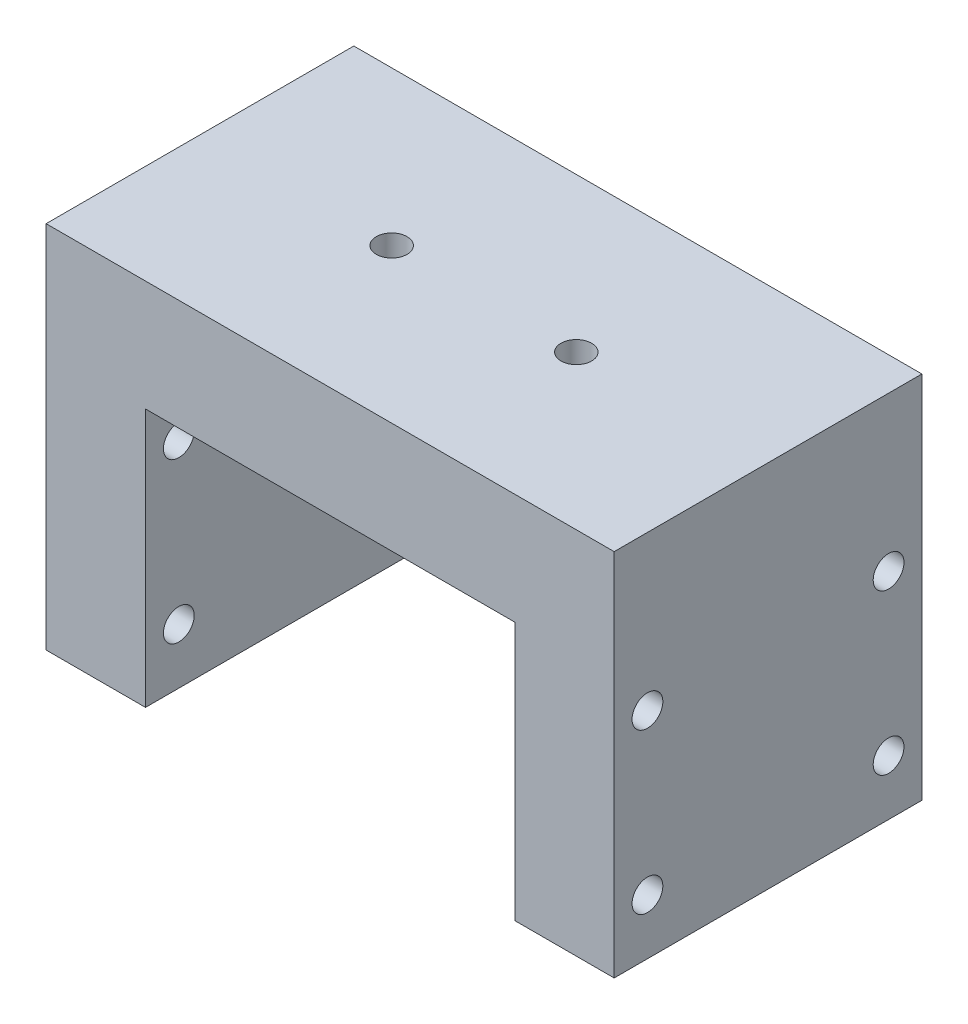
SolidWorks part; units mm, degrees
material "6061 Alloy"
ref_plane "Front Plane" through (0, 0, 0) normal (0, 0, 1) x (1, 0, 0)
ref_plane "Top Plane" through (0, 0, 0) normal (0, 1, 0) x (1, 0, 0)
ref_plane "Right Plane" through (0, 0, 0) normal (1, 0, 0) x (0, 0, -1)
sketch "Sketch2" plane through (0, 0, 0) normal (0, 0, 1) x (1, 0, 0)
  line L0 (-23.075, -21) -> (-23.075, 9)
  line L1 (-23.075, 9) -> (23.075, 9)
  line L2 (23.075, 9) -> (23.075, -21)
  line L3 (23.075, -21) -> (15, -21)
  line L4 (15, -21) -> (15, 0)
  line L5 (15, 0) -> (-15, 0)
  line L6 (-15, 0) -> (-15, -21)
  line L7 (-15, -21) -> (-23.075, -21)
  point P2 (0, 0)
  dimension "D1" = 30
  dimension "D2" = 21
  dimension "D3" = 46.15
  dimension "D4" = 30
extrude "Boss-Extrude1" add sketch "Sketch2" along normal mid plane 25
hole_wizard "M3x0.5 Tapped Hole1" positions "Sketch3" profile "Sketch4" tap size "M3x0.5" standard "ANSI Metric"
sketch "Sketch3" plane through (0, 9, 0) normal (0, 1, 0) x (1, 0, 0)
  line L0 (-7.5, 0) -> (7.5, 0) construction
  point P0 (-7.5, 0)
  point P2 (7.5, 0)
  point P9 (0, 0)
  dimension "D1" = 15
sketch "Sketch4" plane through (-7.5, 9, 0) normal (1, 0, 0) x (0, 0, 1)
  line L0 (0, 0) -> (0, 8.7511)
  line L1 (0, 8.7511) -> (1.25, 8)
  line L2 (1.25, 8) -> (1.25, 0)
  line L5 (1.25, 0) -> (0, 0)
  line L10 (0, 8.7511) -> (-1.25, 8) construction
  line L11 (0, -6.35) -> (0, 107.95) construction
  dimension "Tap Drill Dia." = 2.5
  dimension "Tap Drill Depth" = 8
  dimension "Drill Angle" = 118
cosmetic thread "Hole Thread1" parameters "D1"=6, "D2"=3
cosmetic thread "Hole Thread2" parameters "D1"=6, "D2"=3
hole_wizard "Ø2.5mm Dowel Hole1" positions "Sketch6" profile "Sketch7" hole size "Ø2.5" standard "ANSI Metric" end condition through all
sketch "Sketch6" plane through (-23.075, 0, 0) normal (-1, 0, 0) x (0, 0, 1)
  line L1 (-9.795, -3.53) -> (9.795, -3.53) construction
  line L2 (-9.795, -3.53) -> (-9.795, -16.5) construction
  line L3 (-9.795, -16.5) -> (9.795, -16.5) construction
  line L4 (9.795, -3.53) -> (9.795, -16.5) construction
  line L5 (12.5, -21) -> (-12.5, -21) construction
  point P0 (-9.795, -3.53)
  point P1 (9.795, -16.5)
  point P4 (-9.795, -16.5)
  point P5 (9.795, -3.53)
  point P32 (0, -3.53)
  dimension "D1" = 4.5
  dimension "D2" = 19.59
  dimension "D3" = 12.97
sketch "Sketch7" plane through (-23.075, -3.53, -9.795) normal (0, 1, 0) x (0, 0, 1)
  line L0 (0, 0) -> (0, 46.15)
  line L1 (0, 46.15) -> (1.25, 46.15)
  line L2 (1.25, 46.15) -> (1.25, 0)
  line L5 (1.25, 0) -> (0, 0)
  line L11 (0, -6.35) -> (0, 107.95) construction
  dimension "Thru Hole Dia." = 2.5
  dimension "Thru Hole Depth" = 46.15
